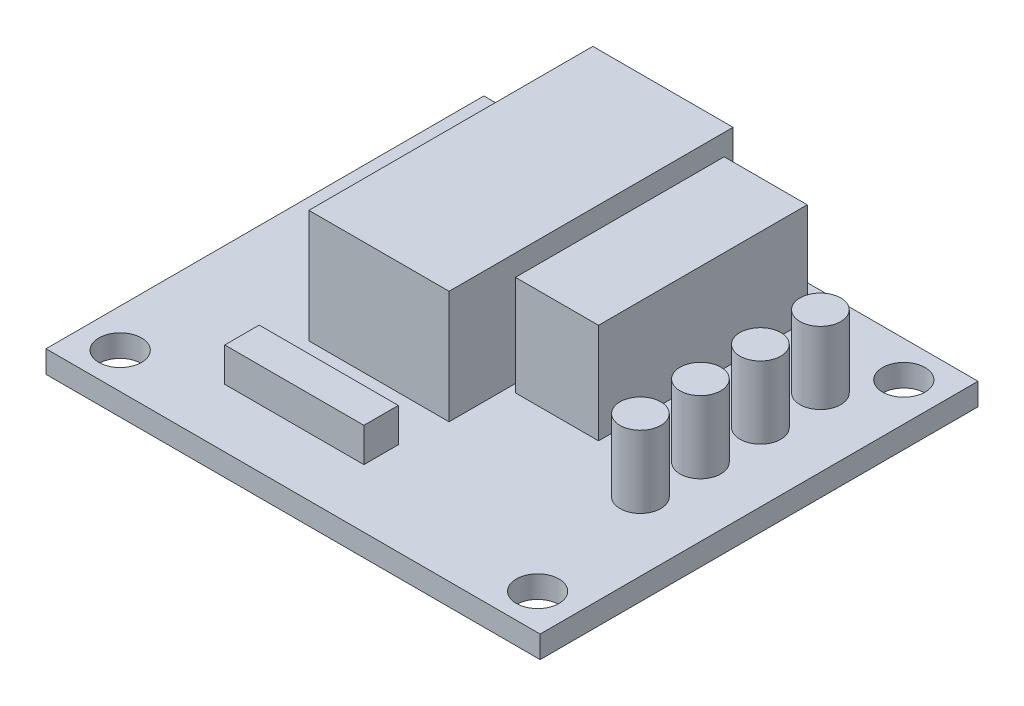
SolidWorks part; units mm, degrees
ref_plane "Front Plane" through (0, 0, 0) normal (0, 0, 1) x (1, 0, 0)
ref_plane "Top Plane" through (0, 0, 0) normal (0, 1, 0) x (1, 0, 0)
ref_plane "Right Plane" through (0, 0, 0) normal (1, 0, 0) x (0, 0, -1)
sketch "Sketch1" plane through (0, 0, 0) normal (0, 1, 0) x (1, 0, 0)
  line L0 (-5.3226, 0) -> (5.3226, 0) construction
  line L1 (-17.6784, 15.6654) -> (17.6784, 15.6654)
  line L2 (-17.6784, 15.6654) -> (-17.6784, -15.6655)
  line L3 (-17.6784, -15.6655) -> (17.6784, -15.6655)
  line L4 (17.6784, 15.6654) -> (17.6784, -15.6655)
  line L5 (-17.6784, 15.6654) -> (17.6784, -15.6655) construction
  line L6 (-17.6784, -15.6655) -> (17.6784, 15.6654) construction
  line L7 (0, -5.3226) -> (0, 5.3226) construction
  circle A0 centre (14.9352, -13.1001) radius 1.524
  circle A1 centre (14.9352, 13.1001) radius 1.524
  circle A2 centre (-14.9352, -13.1001) radius 1.524
  circle A3 centre (-14.9352, 13.1001) radius 1.524
  point P0 (0, 0)
  point P8 (16.4592, -13.1001)
  point P9 (14.9352, -14.6241)
  dimension "D3" = 3.048
  dimension "D1" = 31.3309
  dimension "D2" = 35.3568
  dimension "D4" = 1.0414
  dimension "D5" = 1.2192
extrude "Boss-Extrude1" add sketch "Sketch1" along normal blind 1.5875
sketch "Sketch2" plane through (0, 1.5875, 0) normal (0, 1, 0) x (1, 0, 0)
  line L0 (17.6784, 15.6654) -> (-17.6784, 15.6654) construction
  line L1 (-12.1666, 0.3365) -> (-9.7028, 0.3365)
  line L2 (-12.1666, 0.3365) -> (-12.1666, 10.2933)
  line L3 (-12.1666, 10.2933) -> (-9.7028, 10.2933)
  line L4 (-9.7028, 0.3365) -> (-9.7028, 10.2933)
  line L5 (-12.1666, 0.3365) -> (-9.7028, 10.2933) construction
  line L6 (-12.1666, 10.2933) -> (-9.7028, 0.3365) construction
  line L7 (-9.0805, -9.0107) -> (0.8763, -9.0107)
  line L8 (-9.0805, -9.0107) -> (-9.0805, -11.4745)
  line L9 (-9.0805, -11.4745) -> (0.8763, -11.4745)
  line L10 (0.8763, -9.0107) -> (0.8763, -11.4745)
  line L11 (-9.0805, -9.0107) -> (0.8763, -11.4745) construction
  line L12 (-9.0805, -11.4745) -> (0.8763, -9.0107) construction
  line L13 (-17.6784, 15.6654) -> (-17.6784, -15.6655) construction
  line L14 (-17.6784, -15.6655) -> (17.6784, -15.6655) construction
  point P0 (-10.9347, 5.3149)
  point P5 (-4.1021, -10.2426)
  dimension "D1" = 9.9568
  dimension "D2" = 2.4638
  dimension "D3" = 5.3721
  dimension "D4" = 5.5118
  dimension "D5" = 4.191
  dimension "D6" = 8.5979
extrude "Boss-Extrude2" add sketch "Sketch2" along normal blind 2.4384
sketch "Sketch3" plane through (0, 1.5875, 0) normal (0, 1, 0) x (1, 0, 0)
  line L0 (17.6784, 15.6654) -> (-17.6784, 15.6654) construction
  line L1 (-8.763, 14.5478) -> (1.27, 14.5478)
  line L2 (-8.763, 14.5478) -> (-8.763, -5.7722)
  line L3 (-8.763, -5.7722) -> (1.27, -5.7722)
  line L4 (1.27, 14.5478) -> (1.27, -5.7722)
  line L5 (-17.6784, 15.6654) -> (-17.6784, -15.6655) construction
  point P4 (-8.5685, 14.0623)
  dimension "D1" = 20.32
  dimension "D2" = 10.033
  dimension "D3" = 1.1176
  dimension "D4" = 8.9154
extrude "Boss-Extrude3" add sketch "Sketch3" along normal blind 8.0899
sketch "Sketch4" plane through (0, 1.5875, 0) normal (0, 1, 0) x (1, 0, 0)
  line L0 (17.6784, 15.6654) -> (-17.6784, 15.6654) construction
  line L1 (1.8542, 13.3286) -> (7.7978, 13.3286)
  line L2 (1.8542, 13.3286) -> (1.8542, -1.6066)
  line L3 (1.8542, -1.6066) -> (7.7978, -1.6066)
  line L4 (7.7978, 13.3286) -> (7.7978, -1.6066)
  line L5 (17.6784, -15.6655) -> (17.6784, 15.6654) construction
  dimension "D1" = 14.9352
  dimension "D2" = 5.9436
  dimension "D3" = 2.3368
  dimension "D4" = 9.8806
extrude "Boss-Extrude4" add sketch "Sketch4" along normal blind 7.1628
sketch "Sketch5" plane through (0, 1.5875, 0) normal (0, 1, 0) x (1, 0, 0)
  line L0 (17.6784, 15.6654) -> (-17.6784, 15.6654) construction
  line L1 (17.6784, -15.6655) -> (17.6784, 15.6654) construction
  circle A0 centre (12.7635, 9.3027) radius 1.4605
  circle A1 centre (12.7635, 5.0101) radius 1.4605
  circle A2 centre (12.7635, 0.7175) radius 1.4605
  circle A3 centre (12.7635, -3.5751) radius 1.4605
  point P3 (14.224, 9.3027)
  point P9 (12.7635, 10.7632)
  dimension "D1" = 2.921
  dimension "D3" = 4.2926
  dimension "D4" = 4.9022
  dimension "D5" = 3.4544
  dimension "D2" = 4
extrude "Boss-Extrude5" add sketch "Sketch5" along normal blind 5.1562
